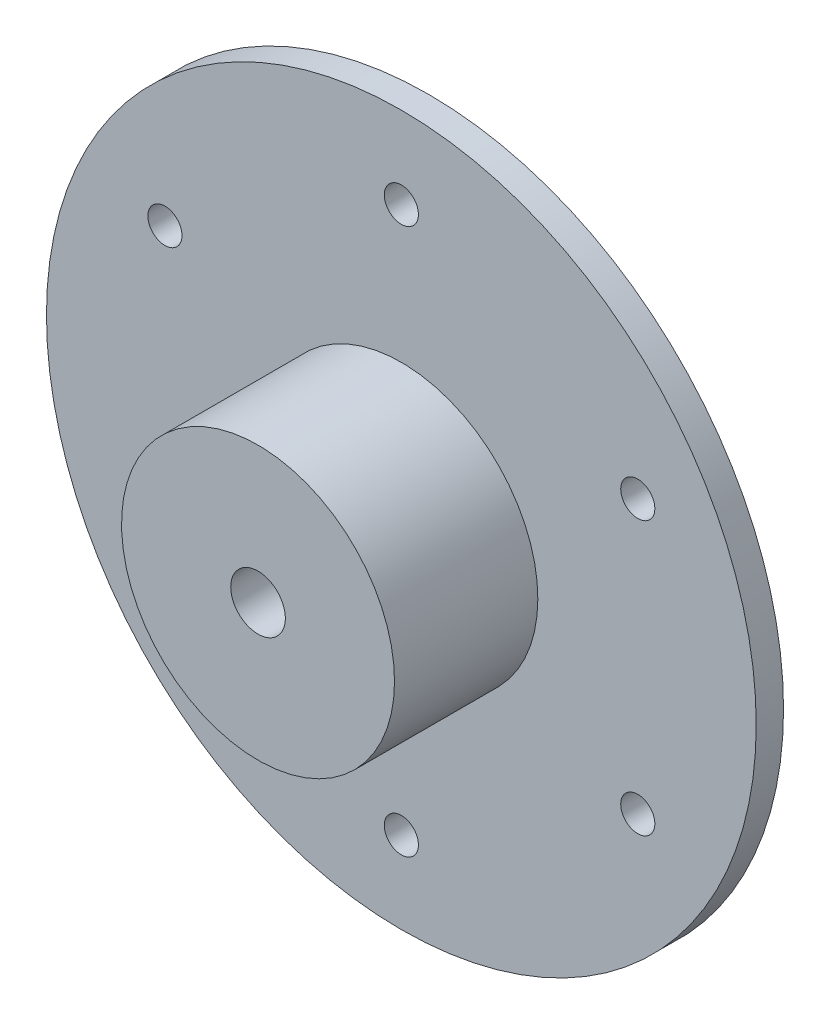
SolidWorks part; units mm, degrees
ref_plane "Front Plane" through (0, 0, 0) normal (0, 0, 1) x (1, 0, 0)
ref_plane "Top Plane" through (0, 0, 0) normal (0, 1, 0) x (1, 0, 0)
ref_plane "Right Plane" through (0, 0, 0) normal (1, 0, 0) x (0, 0, -1)
sketch "Sketch1" plane through (0, 0, 0) normal (1, 0, 0) x (0, 0, -1)
  line L0 (0, 0) -> (0, 52)
  line L1 (0, 52) -> (4, 52)
  line L2 (4, 52) -> (4, 20)
  line L3 (4, 20) -> (25, 20)
  line L4 (25, 20) -> (25, 0)
  line L5 (25, 0) -> (0, 0)
  dimension "D1" = 4
  dimension "D2" = 20
  dimension "D3" = 52
  dimension "D4" = 21
revolve "Revolve1" add sketch "Sketch1" angle 360 about L5
sketch "Sketch2" plane through (0, 0, 0) normal (0, 0, 1) x (1, 0, 0)
  circle A0 centre (0, 0) radius 20
  circle A1 centre (0, 0) radius 4
  dimension "D1" = 40
  dimension "D2" = 8
extrude "Boss-Extrude1" add sketch "Sketch2" along normal blind 21
sketch "Sketch3" plane through (0, 0, -4) normal (0, 0, -1) x (-1, 0, 0)
  line L0 (0, 0) -> (0, 52) construction
  circle A0 centre (0, 0) radius 52 construction
  circle A1 centre (0, 40) radius 2.5
  circle A2 centre (34.641, 20) radius 2.5
  circle A3 centre (34.641, -20) radius 2.5
  circle A4 centre (0, -40) radius 2.5
  circle A5 centre (-34.641, -20) radius 2.5
  circle A6 centre (-34.641, 20) radius 2.5
  point P20 (0, 0)
  dimension "D1" = 5
  dimension "D2" = 40
  dimension "D3" = 6
extrude "Cut-Extrude2" cut sketch "Sketch3" against normal up to next
sketch "Sketch4" plane through (0, 0, 0) normal (0, 1, 0) x (1, 0, 0)
  line L0 (-20, 0) -> (-20, -21) construction
  circle A0 centre (-10, 0) radius 2
  dimension "D1" = 4
  dimension "D2" = 10
  dimension "D3" = 10
extrude "Cut-Extrude3" cut sketch "Sketch4" against normal up to surface (17.3205 mm away)
